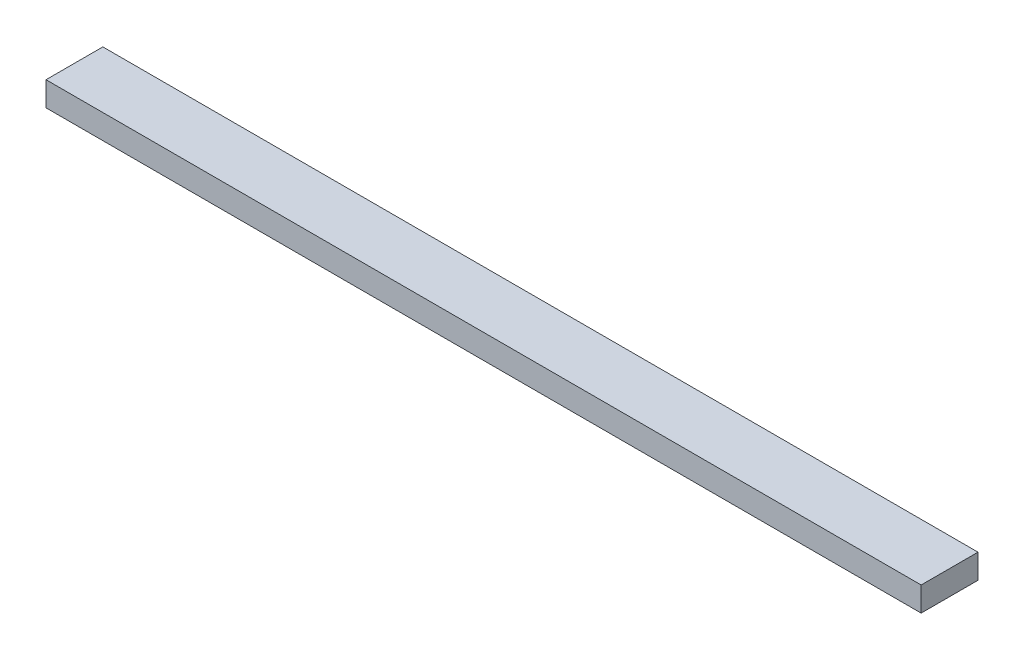
SolidWorks part; units mm, degrees
material "Pine"
ref_plane "Front Plane" through (0, 0, 0) normal (0, 0, 1) x (1, 0, 0)
ref_plane "Top Plane" through (0, 0, 0) normal (0, 1, 0) x (1, 0, 0)
ref_plane "Right Plane" through (0, 0, 0) normal (1, 0, 0) x (0, 0, -1)
sketch "Sketch1" plane through (0, 0, 0) normal (0, 1, 0) x (1, 0, 0)
  line L1 (0, 0) -> (1368.4758, 0)
  line L2 (0, 0) -> (0, 88.9)
  line L3 (0, 88.9) -> (1368.4758, 88.9)
  line L4 (1368.4758, 0) -> (1368.4758, 88.9)
  dimension "D1" = 88.9
  dimension "D2" = 1368.4758
extrude "Boss-Extrude1" add sketch "Sketch1" along normal blind 38.1
